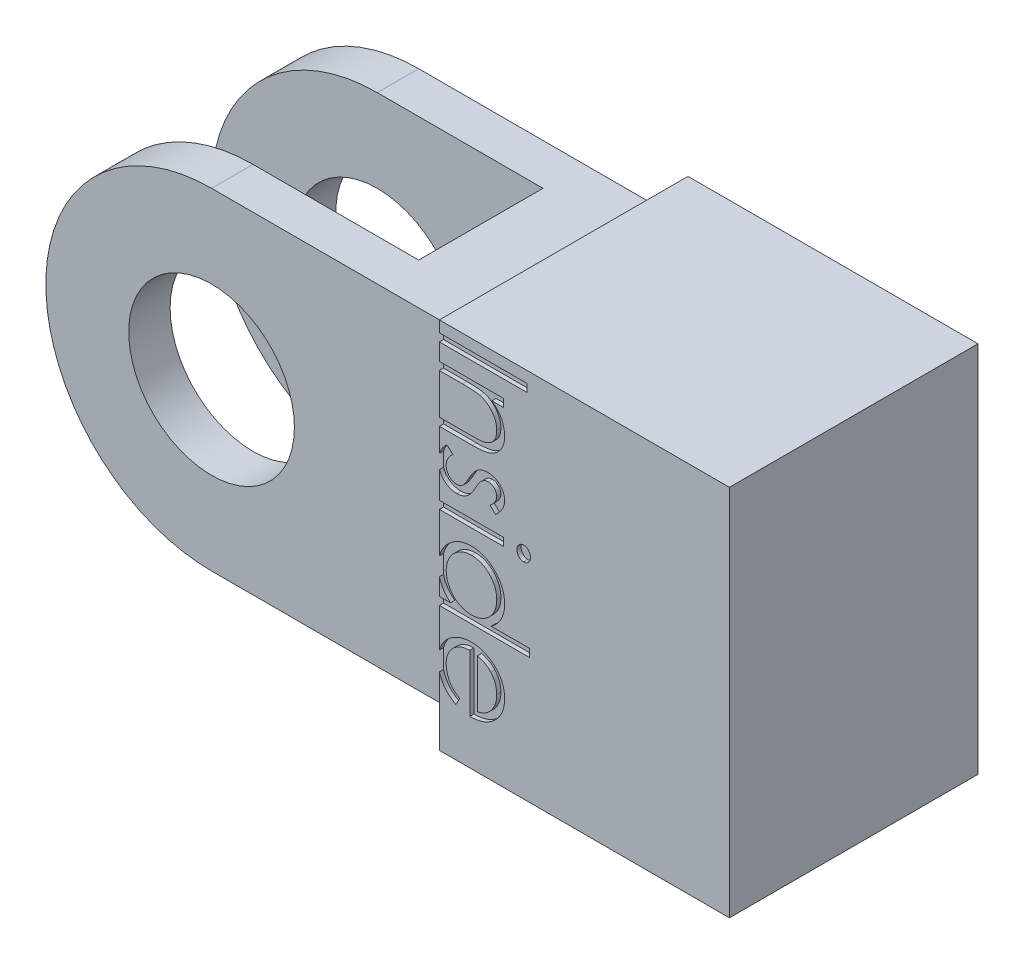
SolidWorks part; units mm, degrees
material "AISI 1020"
ref_plane "Front Plane" through (0, 0, 0) normal (0, 0, 1) x (1, 0, 0)
ref_plane "Top Plane" through (0, 0, 0) normal (0, 1, 0) x (1, 0, 0)
ref_plane "Right Plane" through (0, 0, 0) normal (1, 0, 0) x (0, 0, -1)
sketch "Sketch1" plane through (0, 0, 0) normal (0, 0, 1) x (1, 0, 0)
  line L1 (0, 0) -> (-100, 0)
  line L2 (0, 0) -> (0, 80)
  line L3 (0, 80) -> (-100, 80)
  line L4 (-100, 0) -> (-100, 80)
  arc A0 (-60, 80) -> (-60, 0) centre (-60, 40) ccw
  dimension "D1" = 100
  dimension "D2" = 80
extrude "Boss-Extrude1" add sketch "Sketch1" along normal mid plane 50 contours L3 A0 L1 L2
sketch "Sketch2" plane through (0, 0, 25) normal (0, 0, 1) x (1, 0, 0)
  circle A0 centre (-60, 40) radius 20
  arc A1 (-60, 80) -> (-60, 0) centre (-60, 40) ccw construction
  dimension "D1" = 40
extrude "Cut-Extrude1" cut sketch "Sketch2" against normal through all
sketch "Sketch3" plane through (0, 0, 0) normal (0, 0, 1) x (1, 0, 0)
  line L0 (0, 80) -> (-60, 80) construction
  line L1 (-20, 80) -> (-100, 80)
  line L2 (-20, 80) -> (-20, 0)
  line L3 (-20, 0) -> (-100, 0)
  line L4 (-100, 80) -> (-100, 0)
  line L5 (0, 0) -> (0, 80) construction
  arc A0 (-60, 80) -> (-60, 0) centre (-60, 40) ccw construction
  dimension "D1" = 20
extrude "Cut-Extrude2" cut sketch "Sketch3" against normal mid plane 30
sketch "Sketch4" plane through (0, 0, 0) normal (1, 0, 0) x (0, 0, -1)
  line L10 (30, -5) -> (30, 85)
  line L11 (30, 85) -> (-30, 85)
  line L12 (-30, 85) -> (-30, -5)
  line L13 (-30, -5) -> (30, -5)
  line L14 (30, -5) -> (30, 85)
  line L15 (30, 85) -> (-30, 85)
  line L16 (-30, 85) -> (-30, -5)
  line L17 (-30, -5) -> (30, -5)
  dimension "D1" = 5
extrude "Boss-Extrude2" add sketch "Sketch4" along normal blind 70
sketch "Sketch5" plane through (0, 0, 30) normal (0, 0, 1) x (1, 0, 0)
  text T0 "Inside" font "Century Gothic" height in points 80
extrude "Cut-Extrude3" cut sketch "Sketch5" against normal blind 1
sketch "Sketch6" plane through (0, 0, -30) normal (0, 0, -1) x (-1, 0, 0)
  text T0 "Outside" font "Century Gothic" height in points 80
extrude "Cut-Extrude4" cut sketch "Sketch6" against normal blind 1
